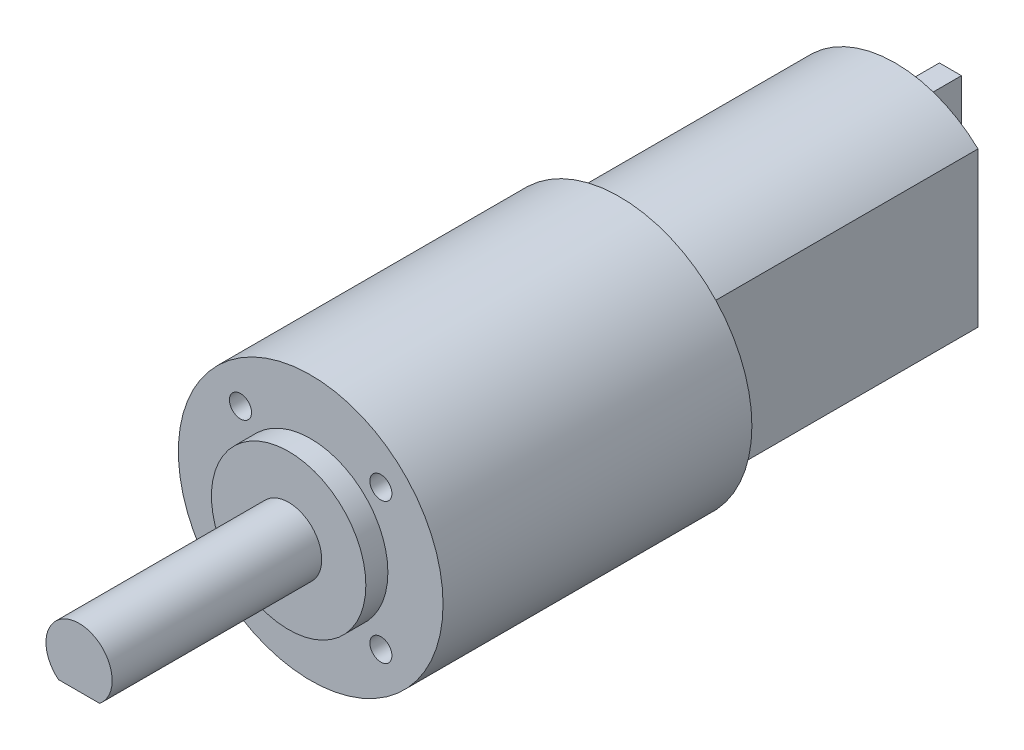
SolidWorks part; units mm, degrees
ref_plane "Front Plane" through (0, 0, 0) normal (0, 0, 1) x (1, 0, 0)
ref_plane "Top Plane" through (0, 0, 0) normal (0, 1, 0) x (1, 0, 0)
ref_plane "Right Plane" through (0, 0, 0) normal (1, 0, 0) x (0, 0, -1)
sketch "Sketch1" plane through (0, 0, 0) normal (0, 0, 1) x (1, 0, 0)
  line L0 (-7.5, 0) -> (7.5, 0) construction
  line L1 (7.5, -7) -> (-7.5, -7) construction
  line L2 (7.5, -7) -> (7.5, 7)
  line L3 (7.5, 7) -> (-7.5, 7) construction
  line L4 (-7.5, -7) -> (-7.5, 7)
  line L5 (7.5, -7) -> (-7.5, 7) construction
  line L6 (7.5, 7) -> (-7.5, -7) construction
  arc A0 (-7.5, 7) -> (7.5, 7) centre (0, -0.875) cw
  arc A1 (-7.5, -7) -> (7.5, -7) centre (0, 0.875) ccw
  point P0 (0, 0)
  point P7 (0, 10)
  dimension "D1" = 14
  dimension "D2" = 15
  dimension "D3" = 10
extrude "Boss-Extrude1" add sketch "Sketch1" along normal blind 25
sketch "Sketch2" plane through (0, 0, 0) normal (0, 0, -1) x (-1, 0, 0)
  line L0 (0, 10) -> (0, -10) construction
  line L1 (-7.5, 0) -> (7.5, 0) construction
  line L2 (1, 3) -> (-1, 3)
  line L3 (1, 3) -> (1, 7)
  line L4 (1, 7) -> (-1, 7)
  line L5 (-1, 3) -> (-1, 7)
  line L6 (1, 3) -> (-1, 7) construction
  line L7 (1, 7) -> (-1, 3) construction
  line L8 (-7.5, -7) -> (-7.5, 7) construction
  line L9 (7.5, 7) -> (7.5, -7) construction
  line L10 (1, -7) -> (-1, -7)
  line L11 (-1, -3) -> (-1, -7)
  line L12 (1, -3) -> (-1, -3)
  line L13 (1, -3) -> (1, -7)
  arc A0 (7.5, 7) -> (-7.5, 7) centre (0, -0.875) ccw construction
  arc A1 (-7.5, -7) -> (7.5, -7) centre (0, 0.875) ccw construction
  point P8 (0, 5)
  dimension "D1" = 2
  dimension "D2" = 4
  dimension "D3" = 3
extrude "Boss-Extrude2" add sketch "Sketch2" along normal blind 5
sketch "Sketch3" plane through (0, 0, 25) normal (0, 0, 1) x (1, 0, 0)
  circle A0 centre (0, 0) radius 12
  dimension "D1" = 24
extrude "Boss-Extrude3" add sketch "Sketch3" along normal blind 28
sketch "Sketch4" plane through (0, 0, 53) normal (0, 0, 1) x (1, 0, 0)
  circle A0 centre (0, 0) radius 7
  dimension "D1" = 14
extrude "Boss-Extrude4" add sketch "Sketch4" along normal blind 2
sketch "Sketch5" plane through (0, 0, 53) normal (0, 0, 1) x (1, 0, 0)
  line L0 (0, 0) -> (-6.364, 6.364) construction
  line L1 (0, 0) -> (6.364, -6.364) construction
  line L2 (-6.364, -6.364) -> (6.364, 6.364) construction
  line L3 (-12, 0) -> (12, 0) construction
  circle A1 centre (-6.364, 6.364) radius 1
  circle A2 centre (6.364, 6.364) radius 1
  circle A3 centre (6.364, -6.364) radius 1
  circle A4 centre (-6.364, -6.364) radius 1
  circle A5 centre (0, 0) radius 12 construction
  point P14 (8.0827, -8.0827)
  point P16 (5.1627, -5.1627)
  dimension "D6" = 2
  dimension "D7" = 2
  dimension "D8" = 2
  dimension "D9" = 2
  dimension "D1" = 9
  dimension "D2" = 18
  dimension "D3" = 9
  dimension "D4" = 45
  dimension "D5" = 45
  dimension "D10" = 9
extrude "Cut-Extrude1" cut sketch "Sketch5" against normal blind 5
sketch "Sketch6" plane through (0, 0, 55) normal (0, 0, 1) x (1, 0, 0)
  line L0 (-1.8576, -2.3557) -> (1.8576, -2.3557)
  arc A0 (1.8576, -2.3557) -> (-1.8576, -2.3557) centre (0, 0) ccw
  dimension "D1" = 6
  dimension "D2" = 3.7152
extrude "Boss-Extrude5" add sketch "Sketch6" along normal blind 19
